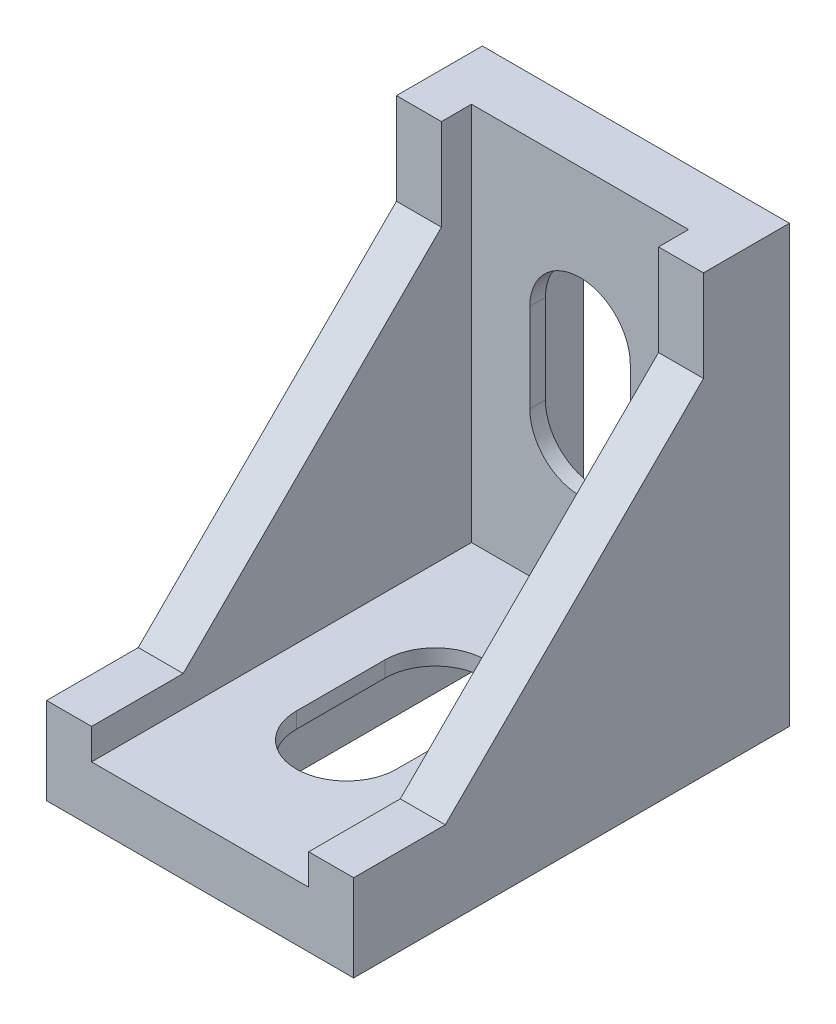
SolidWorks part; units mm, degrees
material "1060 合金"
ref_plane "前视基准面" through (0, 0, 0) normal (0, 0, 1) x (1, 0, 0)
ref_plane "上视基准面" through (0, 0, 0) normal (0, 1, 0) x (1, 0, 0)
ref_plane "右视基准面" through (0, 0, 0) normal (1, 0, 0) x (0, 0, -1)
sketch "草图1" plane through (0, 0, 0) normal (0, 0, 1) x (1, 0, 0)
  line L1 (0, 0) -> (19.8, 0)
  line L2 (0, 0) -> (0, -28.1)
  line L3 (0, -28.1) -> (19.8, -28.1)
  line L4 (19.8, 0) -> (19.8, -28.1)
  dimension "D1" = 19.8
  dimension "D2" = 28.1
extrude "凸台-拉伸1" add sketch "草图1" along normal blind 3.6 contours L1 L4 L3 L2
sketch "草图2" plane through (0, 0, 3.6) normal (0, 0, 1) x (1, 0, 0)
  line L0 (0, -28.1) -> (19.8, -28.1) construction
  line L1 (0, 0) -> (2.9, 0)
  line L2 (0, 0) -> (0, -28.1)
  line L3 (0, -28.1) -> (2.9, -28.1)
  line L4 (2.9, 0) -> (2.9, -28.1)
  line L5 (9.9, 4.0964) -> (9.9, -33.1846) construction
  line L6 (19.8, -28.1) -> (16.9, -28.1)
  line L7 (16.9, 0) -> (16.9, -28.1)
  line L8 (19.8, 0) -> (16.9, 0)
  line L9 (19.8, 0) -> (19.8, -28.1)
  dimension "D1" = 2.9
  dimension "D2" = 9.9
extrude "凸台-拉伸2" add sketch "草图2" along normal blind 1.94
sketch "草图3" plane through (0, 0, 3.6) normal (0, 0, 1) x (1, 0, 0)
  line L0 (19.8, -28.1) -> (19.8, 0) construction
  line L1 (0, -28.1) -> (19.8, -28.1)
  line L2 (0, -28.1) -> (0, -24.48)
  line L3 (0, -24.48) -> (19.8, -24.48)
  line L4 (19.8, -28.1) -> (19.8, -24.48)
  dimension "D1" = 3.62
extrude "凸台-拉伸3" add sketch "草图3" along normal blind 27.8
sketch "草图4" plane through (0, 0, 5.54) normal (0, 0, 1) x (1, 0, 0)
  line L0 (0, 0) -> (0, -24.48) construction
  line L1 (0, -22.5) -> (2.9, -22.5)
  line L2 (0, -22.5) -> (0, -28.1)
  line L3 (0, -28.1) -> (2.9, -28.1)
  line L4 (2.9, -22.5) -> (2.9, -28.1)
  line L5 (0, -28.1) -> (19.8, -28.1) construction
  line L6 (16.9, 0) -> (16.9, -24.48) construction
  line L7 (16.9, -22.5) -> (19.8, -22.5)
  line L8 (16.9, -22.5) -> (16.9, -28.1)
  line L9 (16.9, -28.1) -> (19.8, -28.1)
  line L10 (19.8, -22.5) -> (19.8, -28.1)
  dimension "D1" = 5.6
extrude "凸台-拉伸4" add sketch "草图4" along normal blind 25.86
sketch "草图5" plane through (0, 0, 5.54) normal (0, 0, 1) x (1, 0, 0)
  line L0 (0, 0) -> (0, -22.5) construction
  line L1 (0, -5.9) -> (2.9, -5.9)
  line L2 (0, -5.9) -> (0, -28.1)
  line L3 (0, -28.1) -> (2.9, -28.1)
  line L4 (2.9, -5.9) -> (2.9, -28.1)
  line L5 (0, -28.1) -> (19.8, -28.1) construction
  line L6 (16.9, 0) -> (16.9, -24.48) construction
  line L7 (0, -5.9) -> (2.9, -5.9)
  line L8 (0, -5.9) -> (0, -22.5)
  line L9 (0, -22.5) -> (2.9, -22.5)
  line L10 (2.9, -5.9) -> (2.9, -22.5)
  line L11 (16.9, -5.9) -> (19.8, -5.9)
  line L12 (16.9, -5.9) -> (16.9, -22.5)
  line L13 (16.9, -22.5) -> (19.8, -22.5)
  line L14 (19.8, -5.9) -> (19.8, -22.5)
  line M5 (0, 0) -> (0, -22.5)
  line M6 (0, -22.5) -> (2.9, -22.5)
  line M7 (2.9, -22.5) -> (2.9, 0)
  dimension "D1" = 22.2
extrude "凸台-拉伸5" add sketch "草图5" along normal blind 16.65 contours L1 M5 M6 M7 | L14 L11 L12 L13
sketch "草图6" plane through (0, 0, 31.4) normal (0, 0, 1) x (1, 0, 0)
  line L0 (0, -22.5) -> (0, -28.1)
  line L1 (0, -28.1) -> (19.8, -28.1)
  line L2 (19.8, -28.1) -> (19.8, -22.5)
  line L3 (19.8, -22.5) -> (16.9, -22.5)
  line L4 (16.9, -22.5) -> (16.9, -24.48)
  line L5 (16.9, -24.48) -> (2.9, -24.48)
  line L6 (2.9, -24.48) -> (2.9, -22.5)
  line L7 (2.9, -24.48) -> (2.9, 0) construction
  line L8 (2.9, -24.48) -> (2.9, -22.5) construction
  line L9 (2.9, -22.5) -> (0, -22.5)
extrude "切除-拉伸1" cut sketch "草图6" against normal blind 3.3
sketch "草图7" plane through (0, 0, 0) normal (-1, 0, 0) x (0, 0, 1)
  line L0 (5.54, -5.9) -> (22.19, -5.9)
  line L1 (22.19, -22.5) -> (22.19, -5.9)
  line L2 (5.54, -5.9) -> (22.19, -22.5)
  line L8 (28.1, -28.1) -> (28.1, -22.5)
  line L9 (28.1, -22.5) -> (22.19, -22.5)
  line L10 (22.19, -22.5) -> (22.19, -5.9)
  line L11 (22.19, -5.9) -> (5.54, -5.9)
  line L12 (5.54, -5.9) -> (5.54, 0)
  line L13 (5.54, 0) -> (0, 0)
  line L14 (0, 0) -> (0, -28.1)
  line L15 (0, -28.1) -> (28.1, -28.1)
  line L16 (28.1, -28.1) -> (28.1, -22.5)
  line L17 (28.1, -22.5) -> (22.19, -22.5)
  line L18 (22.19, -22.5) -> (22.19, -5.9)
  line L19 (22.19, -5.9) -> (5.54, -5.9)
  line L20 (5.54, -5.9) -> (5.54, 0)
  line L21 (5.54, 0) -> (0, 0)
  line L22 (0, 0) -> (0, -28.1)
  line L23 (0, -28.1) -> (28.1, -28.1)
  dimension "D1" = 0
sketch "草图9" plane through (0, 0, 0) normal (-1, 0, 0) x (0, 0, 1)
  line L0 (5.54, -5.9) -> (22.19, -5.9)
  line L1 (22.19, -5.9) -> (22.19, -22.5)
  line L2 (22.19, -22.5) -> (5.54, -5.9)
extrude "切除-拉伸2" cut sketch "草图9" against normal blind 2.9
sketch "草图10" plane through (19.8, 0, 0) normal (1, 0, 0) x (0, 0, -1)
  line L0 (-5.54, -5.9) -> (-22.19, -5.9)
  line L1 (-22.19, -5.9) -> (-22.19, -22.5)
  line L2 (-22.19, -22.5) -> (-5.54, -5.9)
extrude "切除-拉伸3" cut sketch "草图10" against normal blind 2.9
sketch "草图11" plane through (0, -28.1, 0) normal (0, -1, 0) x (1, 0, 0)
  line L0 (9.9, 28.908) -> (9.9, -2.1129) construction
  line L1 (0, 28.1) -> (19.8, 28.1) construction
  line L2 (6.525, 23.7) -> (13.275, 23.7)
  line L3 (6.525, 23.7) -> (6.525, 8.1)
  line L4 (6.525, 8.1) -> (13.275, 8.1)
  line L5 (13.275, 23.7) -> (13.275, 8.1)
  dimension "D1" = 6.75
  dimension "D2" = 15.6
  dimension "D3" = 9.9
  dimension "D4" = 3.375
  dimension "D5" = 4.4
extrude "切除-拉伸4" cut sketch "草图11" against normal blind 2.6
sketch "草图13" plane through (13.275, 0, 0) normal (-1, 0, 0) x (0, 0, 1)
  line L0 (8.1, -25.5) -> (5.5, -28.1)
  line L1 (8.1, -28.1) -> (5.5, -28.1)
  line L2 (8.1, -28.1) -> (8.1, -25.5)
  line L3 (8.1, -25.5) -> (5.5, -25.5)
  line L4 (5.5, -28.1) -> (5.5, -25.5)
  line M4 (8.1, -25.5) -> (8.1, -28.1)
  dimension "D1" = 2.6
  dimension "D2" = 2.6
extrude "切除-拉伸5" cut sketch "草图13" along normal blind 6.75 contours L1 L0 M4
sketch "草图14" plane through (0, 0, 0) normal (-1, 0, 0) x (0, 0, 1)
  line L0 (0, -28.1) -> (22.19, -5.9) construction
ref_plane "基准面4" through (0, -14.0437, 14.05) normal (0, -0.7069, 0.7073) x (0, 0.7073, 0.7069)
mirror "镜向1" about plane through (0, -14.0437, 14.05) normal (0, -0.7069, 0.7073) of "切除-拉伸5", "切除-拉伸4"
sketch "草图16" plane through (0, -25.5, 0) normal (0, -1, 0) x (1, 0, 0)
  line L0 (9.9, 0.011) -> (9.9, 35.7321) construction
  line L1 (6.525, 23.7) -> (13.275, 23.7)
  line L2 (6.525, 23.7) -> (6.525, 8.1)
  line L3 (6.525, 8.1) -> (13.275, 8.1)
  line L4 (13.275, 23.7) -> (13.275, 8.1)
  line L5 (9.9, 28.1) -> (9.9, 21.9)
  line L6 (0, 28.1) -> (19.8, 28.1) construction
  line L7 (9.9, 21.9) -> (9.9, 18.66)
  line L8 (9.9, 21.9) -> (9.9, 8.1)
  line L9 (9.9, 21.9) -> (9.9, 9.7)
  line L10 (9.9, 9.7) -> (9.9, 12.94)
  line L11 (9.9, 9.7) -> (9.9, 12.94)
  line L12 (6.66, 18.66) -> (6.66, 12.94)
  line L13 (13.14, 12.94) -> (13.14, 18.66)
  line L15 (8.06, 23.7) -> (11.74, 23.7)
  line L16 (8.06, 23.7) -> (8.06, 25.36)
  line L17 (8.06, 25.36) -> (11.74, 25.36)
  line L18 (11.74, 23.7) -> (11.74, 25.36)
  line L19 (8.06, 25.36) -> (11.74, 25.36)
  line L20 (8.06, 25.36) -> (8.06, 23.7)
  line L21 (8.06, 23.7) -> (11.74, 23.7)
  line L22 (11.74, 25.36) -> (11.74, 23.7)
  circle A0 centre (9.9, 18.66) radius 3.24
  circle A1 centre (9.9, 12.94) radius 3.24
  arc A2 (6.66, 12.94) -> (13.14, 12.94) centre (9.9, 12.94) ccw
  arc A3 (13.14, 18.66) -> (6.66, 18.66) centre (9.9, 18.66) ccw
  dimension "D1" = 6.2
  dimension "D2" = 3.24
  dimension "D3" = 12.2
  dimension "D4" = 3.24
  dimension "D5" = 1.84
  dimension "D6" = 3.68
  dimension "D7" = 1.66
extrude "切除-拉伸6" cut sketch "草图16" against normal blind 5 contours L13 A3 L12 A2
sketch "草图17" plane through (0, -28.1, 0) normal (0, -1, 0) x (1, 0, 0)
  line L0 (10.1326, 27.6129) -> (10.1326, -3.2598) construction
  line L1 (13.275, 23.7) -> (6.525, 23.7) construction
  line L2 (8.1326, 23.7) -> (12.1326, 23.7)
  line L3 (8.1326, 23.7) -> (8.1326, 25.7)
  line L4 (8.1326, 25.7) -> (12.1326, 25.7)
  line L5 (12.1326, 23.7) -> (12.1326, 25.7)
  line L6 (8.1326, 5.5) -> (12.1326, 5.5)
  line L7 (8.1326, 3.5) -> (12.1326, 3.5)
  line L8 (8.1326, 3.5) -> (8.1326, 5.5)
  line L9 (12.1326, 3.5) -> (12.1326, 5.5)
  line L10 (6.525, 5.5) -> (13.275, 5.5) construction
  dimension "D1" = 4
  dimension "D2" = 2
  dimension "D3" = 2
  dimension "D4" = 4
  dimension "D5" = 2
  dimension "D6" = 2
  dimension "D7" = 2
sketch "草图18" [suppressed] plane through (0, -28.1, 0) normal (0, -1, 0) x (1, 0, 0)
  line L0 (8.1326, 5.5) -> (8.1326, 3.84)
  line L1 (8.1326, 25.7) -> (12.1326, 25.7)
  line L2 (8.1326, 25.7) -> (8.1326, 23.7)
  line L3 (8.1326, 23.7) -> (12.1326, 23.7)
  line L4 (12.1326, 25.7) -> (12.1326, 23.7)
  line L5 (8.1326, 25.7) -> (12.1326, 25.7)
  line L6 (8.1326, 25.7) -> (8.1326, 23.7)
  line L7 (8.1326, 23.7) -> (12.1326, 23.7)
  line L8 (12.1326, 25.7) -> (12.1326, 23.7)
  line L9 (8.1326, 3.84) -> (11.8126, 3.84)
  line L10 (8.1326, 5.5) -> (11.8126, 5.5)
  line L11 (11.8126, 5.5) -> (11.8126, 3.84)
sketch "草图19" plane through (0, -28.1, 0) normal (0, -1, 0) x (1, 0, 0)
  line L1 (8.1326, 5.5) -> (12.1326, 5.5)
  line L2 (8.1326, 5.5) -> (8.1326, 3.5)
  line L3 (8.1326, 3.5) -> (12.1326, 3.5)
  line L4 (12.1326, 5.5) -> (12.1326, 3.5)
  line L5 (8.1326, 25.7) -> (12.1326, 25.7)
  line L6 (8.1326, 25.7) -> (8.1326, 23.7)
  line L7 (8.1326, 23.7) -> (12.1326, 23.7)
  line L8 (12.1326, 25.7) -> (12.1326, 23.7)
extrude "凸台-拉伸7" add sketch "草图19" along normal blind 2
sketch "草图21" plane through (8.1326, 0, 0) normal (-1, 0, 0) x (0, 0, 1)
  line L0 (25.7, -28.1) -> (23.7, -30.1)
  line L1 (25.7, -30.1) -> (25.7, -28.1)
  line L2 (5.5, -30.1) -> (3.5, -30.1)
  line L3 (3.5, -30.1) -> (5.5, -28.1)
  line L4 (25.7, -28.1) -> (23.7, -28.1)
  line L5 (23.7, -28.1) -> (23.7, -30.1)
  line L6 (23.7, -30.1) -> (25.7, -30.1)
  line L7 (25.7, -30.1) -> (25.7, -28.1)
  line L8 (25.7, -28.1) -> (23.7, -28.1)
  line L9 (23.7, -28.1) -> (23.7, -30.1)
  line L10 (23.7, -30.1) -> (25.7, -30.1)
  line L11 (25.7, -30.1) -> (25.7, -28.1)
  line L12 (5.5, -28.1) -> (5.5, -30.1)
  line M7 (23.7, -30.1) -> (25.7, -30.1)
  line M8 (25.7, -30.1) -> (25.7, -28.1)
  dimension "D1" = 0
extrude "切除-拉伸7" cut sketch "草图21" against normal blind 10 contours L12 L3 L2 | L0 M8 M7
sketch "草图23" plane through (0, 0, 0) normal (0, 0, 1) x (1, 0, 0)
  line L0 (9.9001, -28.0657) -> (9.9001, 7.6554) construction
  line L1 (6.5251, -4.3767) -> (13.2751, -4.3767)
  line L2 (6.5251, -4.3767) -> (6.5251, -19.9767)
  line L3 (6.5251, -19.9767) -> (13.2751, -19.9767)
  line L4 (13.2751, -4.3767) -> (13.2751, -19.9767)
  line L5 (9.9001, 0.0233) -> (9.9001, -6.1767)
  line L6 (9.9001, -6.1767) -> (9.9001, -9.4167)
  line L7 (9.9001, -6.1767) -> (9.9001, -19.9767)
  line L8 (9.9001, -6.1767) -> (9.9001, -18.3767)
  line L9 (9.9001, -18.3767) -> (9.9001, -15.1367)
  line L10 (9.9001, -18.3767) -> (9.9001, -15.1367)
  line L11 (6.6601, -9.4167) -> (6.6601, -15.1367)
  line L12 (13.1401, -15.1367) -> (13.1401, -9.4167)
  line L13 (8.0601, -4.3767) -> (11.7401, -4.3767)
  line L14 (8.0601, -4.3767) -> (8.0601, -2.7167)
  line L15 (8.0601, -2.7167) -> (11.7401, -2.7167)
  line L16 (11.7401, -4.3767) -> (11.7401, -2.7167)
  line L17 (8.0601, -2.7167) -> (11.7401, -2.7167)
  line L18 (8.0601, -2.7167) -> (8.0601, -4.3767)
  line L19 (8.0601, -4.3767) -> (11.7401, -4.3767)
  line L20 (11.7401, -2.7167) -> (11.7401, -4.3767)
  circle A0 centre (9.9001, -9.4167) radius 3.24
  circle A1 centre (9.9001, -15.1367) radius 3.24
  arc A2 (6.6601, -15.1367) -> (13.1401, -15.1367) centre (9.9001, -15.1367) ccw
  arc A3 (13.1401, -9.4167) -> (6.6601, -9.4167) centre (9.9001, -9.4167) ccw
  dimension "D1" = 6.2
  dimension "D2" = 3.24
  dimension "D3" = 12.2
  dimension "D4" = 3.24
  dimension "D5" = 1.84
  dimension "D6" = 3.68
  dimension "D7" = 1.66
extrude "切除-拉伸8" cut sketch "草图23" along normal blind 10 contours A1 A0 L6 L7 | A1 A0 L8 | A0 A1 L8 | L8 A1 A0 | A1 L7 L6 A0 | A0 A1 L8 | A1 L12 A0 | A1 A0 L11
